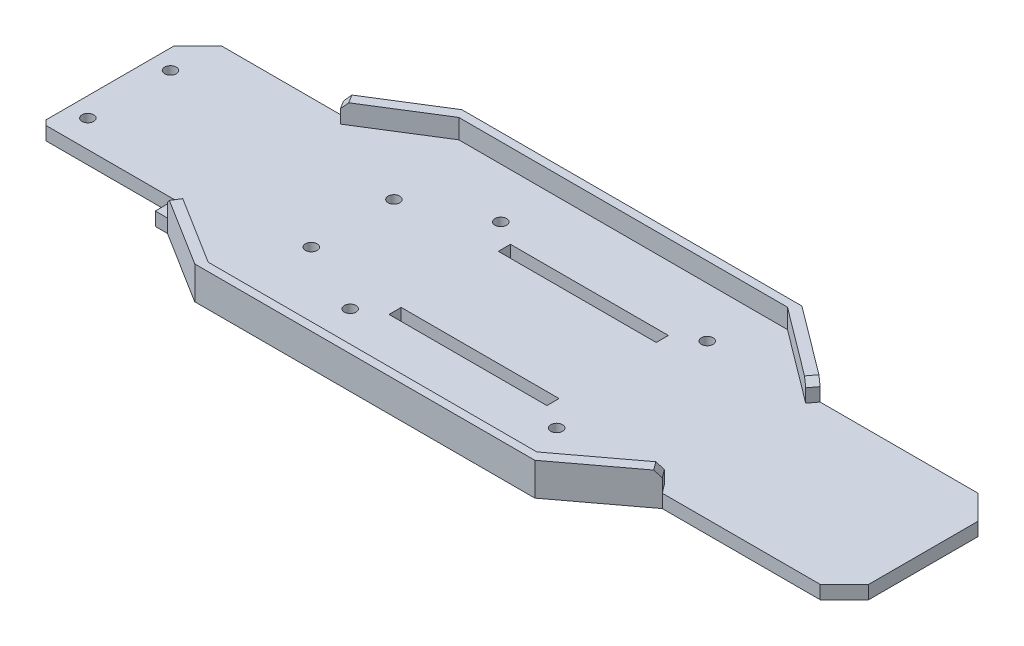
SolidWorks part; units mm, degrees
material "PETG - Polymaker"
ref_plane "Front Plane" through (0, 0, 0) normal (0, 0, 1) x (1, 0, 0)
ref_plane "Top Plane" through (0, 0, 0) normal (0, 1, 0) x (1, 0, 0)
ref_plane "Right Plane" through (0, 0, 0) normal (1, 0, 0) x (0, 0, -1)
sketch "Sketch1" plane through (0, 0, 0) normal (0, 1, 0) x (1, 0, 0)
  line L0 (-235.1499, 0) -> (235.1499, 0) construction
  line L1 (0, 0) -> (0, 52596.8311) construction
  line L2 (-100, 36.25) -> (-70, 55)
  line L3 (-70, 55) -> (70, 55)
  line L4 (-100, 36.25) -> (-160, 36.25)
  line L5 (-160, 36.25) -> (-160, -36.25)
  line L6 (-70, -55) -> (70, -55)
  line L7 (-100, -36.25) -> (-70, -55)
  line L8 (-100, -36.25) -> (-160, -36.25)
  line L9 (70, 55) -> (100, 32.5)
  line L10 (100, 32.5) -> (175, 32.5)
  line L11 (175, 32.5) -> (175, -32.5)
  line L12 (100, -32.5) -> (175, -32.5)
  line L13 (70, -55) -> (100, -32.5)
  point P3 (0, 0)
  point P10 (-85, 45.625)
  point P15 (-85, -45.625)
  point P18 (-160, 0)
  point P19 (0, -55)
  point P20 (0, 55)
  point P23 (175, 0)
  dimension "D1" = 55
  dimension "D2" = 72.5
  dimension "D3" = 30
  dimension "D4" = 60
  dimension "D5" = 140
  dimension "D6" = 75
  dimension "D7" = 65
  dimension "D8" = 30
  dimension "D9" = 110
extrude "Boss-Extrude1" add sketch "Sketch1" along normal blind 5.5
sketch "Sketch3" plane through (0, 5.5, 0) normal (0, 1, 0) x (1, 0, 0)
  line L0 (0, 0) -> (50000, 0) construction
  line L1 (0, 0) -> (0, 50000) construction
  line L2 (0, 55) -> (-70, 55)
  line L3 (70, 55) -> (-70, 55) construction
  line L4 (-70, 55) -> (-100, 36.25)
  line L5 (-100, 36.25) -> (-97.88, 32.858)
  line L6 (-97.88, 32.858) -> (-67.88, 51.608)
  line L7 (-67.88, 51.608) -> (0, 51.608)
  line L8 (-70, 55) -> (-67.88, 51.608) construction
  line L9 (0, 55) -> (70, 55)
  line L10 (70, 55) -> (100, 32.5)
  line L11 (100, 32.5) -> (97.456, 29.108)
  line L12 (97.456, 29.108) -> (67.456, 51.608)
  line L13 (67.456, 51.608) -> (0, 51.608)
  line L14 (67.456, 51.608) -> (70, 55) construction
  line L15 (67.456, -51.608) -> (70, -55) construction
  line L16 (-70, -55) -> (-67.88, -51.608) construction
  line L17 (67.456, -51.608) -> (0, -51.608)
  line L18 (97.456, -29.108) -> (67.456, -51.608)
  line L19 (100, -32.5) -> (97.456, -29.108)
  line L20 (70, -55) -> (100, -32.5)
  line L21 (0, -55) -> (70, -55)
  line L22 (-67.88, -51.608) -> (0, -51.608)
  line L23 (-97.88, -32.858) -> (-67.88, -51.608)
  line L24 (-100, -36.25) -> (-97.88, -32.858)
  line L25 (-70, -55) -> (-100, -36.25)
  line L26 (0, -55) -> (-70, -55)
  dimension "D1" = 4
extrude "Chassis-Walls1" add sketch "Sketch3" along normal blind 8
chamfer "Chamfer1" distance 10 angle 45 2 edges at (-160, 2.75, -36.25) (-160, 2.75, 36.25)
chamfer "Chamfer2" distance 10 angle 45 2 edges at (175, 2.75, -32.5) (175, 2.75, 32.5)
chamfer "Chamfer3" distance 2.5 angle 45 4 edges at (-98.94, 13.5, -34.554) (-98.94, 13.5, 34.554) (98.728, 13.5, 30.804) (98.728, 13.5, -30.804)
sketch "Sketch4" plane through (0, 0, 0) normal (0, -1, 0) x (1, 0, 0)
  line L0 (0, 0) -> (50000, 0) construction
  line L1 (-152, 17) -> (-60, 17) construction
  line L2 (-160, -26.25) -> (-160, 26.25) construction
  circle A0 centre (-152, 17) radius 2.4
  circle A1 centre (-60, 17) radius 2.4
  circle A2 centre (-60, -17) radius 2.4
  circle A3 centre (-152, -17) radius 2.4
  circle A4 centre (-30, 31) radius 2.4
  circle A5 centre (55, 31) radius 2.4
  circle A6 centre (55, -31) radius 2.4
  circle A7 centre (-30, -31) radius 2.4
  dimension "D1" = 4.8
  dimension "D2" = 4.8
  dimension "D6" = 4.8
  dimension "D8" = 4.8
  dimension "D3" = 8
  dimension "D4" = 92
  dimension "D5" = 34
  dimension "D7" = 30
  dimension "D9" = 85
  dimension "D10" = 62
extrude "Cut-Extrude1" cut sketch "Sketch4" against normal blind 10
sketch "Sketch5" plane through (0, 5.5, 0) normal (0, 1, 0) x (1, 0, 0)
  line L0 (-160, -28.25) -> (-105, -28.25)
  line L1 (-160, 26.25) -> (-160, -26.25) construction
  line L2 (-105, -28.25) -> (-105, -36.25)
  line L3 (-150, -36.25) -> (-100, -36.25) construction
  line L4 (-105, -36.25) -> (-160, -36.25)
  line L5 (-160, -36.25) -> (-160, -28.25)
  dimension "D1" = 55
  dimension "D2" = 8
extrude "Cut-Extrude2" cut sketch "Sketch5" against normal blind 10
sketch "Sketch6" plane through (0, 5.5, 0) normal (0, 1, 0) x (1, 0, 0)
  line L0 (0, 0) -> (50000, 0) construction
  line L1 (55, 31) -> (-30, 31) construction
  line L2 (12.5, 30.75) -> (12.5, 50030.75) construction
  line L3 (-20, -20) -> (45, -25) construction
  line L4 (-20, 25) -> (45, 25)
  line L5 (-20, 25) -> (-20, 20)
  line L6 (-20, 20) -> (45, 20)
  line L7 (45, 25) -> (45, 20)
  line L8 (-20, 25) -> (45, 20) construction
  line L9 (-20, 20) -> (45, 25) construction
  line L10 (-20, -25) -> (45, -20) construction
  line L11 (45, -25) -> (45, -20)
  line L12 (-20, -20) -> (45, -20)
  line L13 (-20, -25) -> (-20, -20)
  line L14 (-20, -25) -> (45, -25)
  point P9 (12.5, 31)
  point P10 (12.5, 22.5)
  point P19 (12.5, -22.5)
  dimension "D1" = 5
  dimension "D2" = 65
  dimension "D3" = 20
extrude "Cut-Extrude3" cut sketch "Sketch6" against normal through all
equation "\"D6@Sketch4\"=\"D2@Sketch4\""
equation "\"D8@Sketch4\"=\"D2@Sketch4\""
